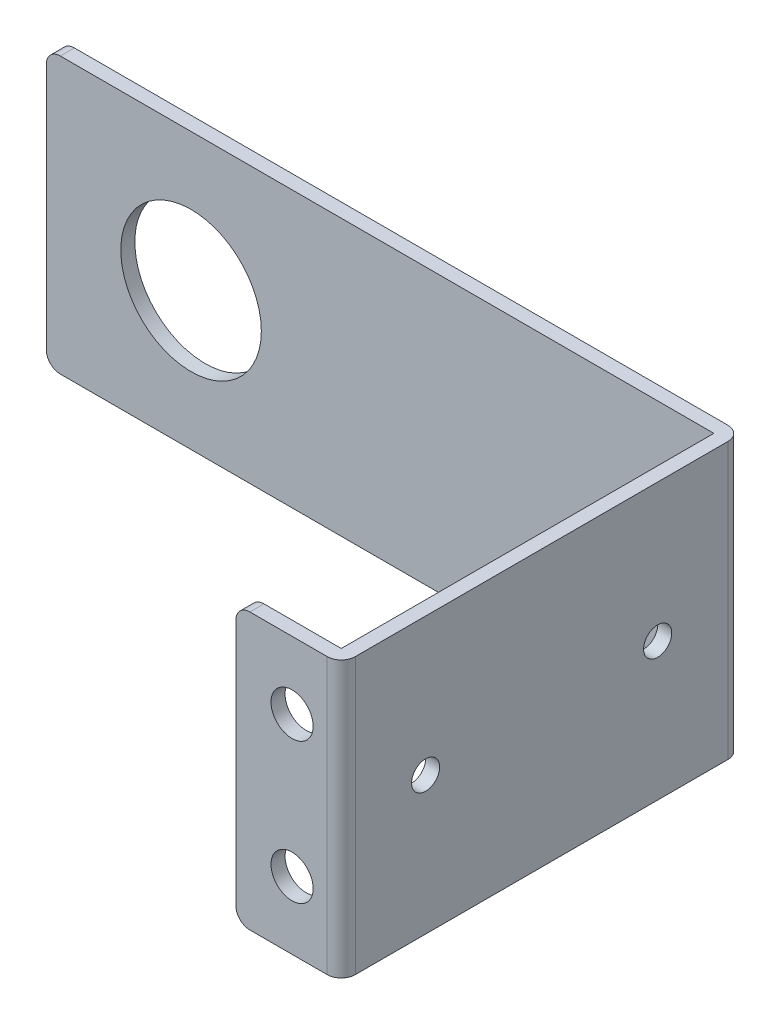
SolidWorks part; units mm, degrees
ref_plane "Front Plane" through (0, 0, 0) normal (0, 0, 1) x (1, 0, 0)
ref_plane "Top Plane" through (0, 0, 0) normal (0, 1, 0) x (1, 0, 0)
ref_plane "Right Plane" through (0, 0, 0) normal (1, 0, 0) x (0, 0, -1)
sketch "Sketch1" plane through (0, 0, 0) normal (0, 0, 1) x (1, 0, 0)
  line L1 (-23.75, -9.8) -> (23.75, -9.8)
  line L2 (-23.75, -9.8) -> (-23.75, 9.8)
  line L3 (-23.75, 9.8) -> (23.75, 9.8)
  line L4 (23.75, -9.8) -> (23.75, 9.8)
  line L5 (-23.75, -9.8) -> (23.75, 9.8) construction
  line L6 (-23.75, 9.8) -> (23.75, -9.8) construction
  circle A0 centre (-13.45, 0) radius 5
  point P0 (0, 0)
  dimension "D5" = 10
  dimension "D1" = 47.5
  dimension "D2" = 19.6
  dimension "D3" = 9.8
  dimension "D4" = 10.3
extrude "Boss-Extrude1" add sketch "Sketch1" along normal blind 1
sketch "Sketch2" plane through (0, 0, 1) normal (0, 0, 1) x (1, 0, 0)
  line L1 (23.75, 9.8) -> (24.75, 9.8)
  line L2 (23.75, 9.8) -> (23.75, -9.8)
  line L3 (23.75, -9.8) -> (24.75, -9.8)
  line L4 (24.75, 9.8) -> (24.75, -9.8)
  dimension "D1" = 1
extrude "Boss-Extrude2" add sketch "Sketch2" along normal blind 28.512 from offset 1 offset against normal yes
sketch "Sketch3" plane through (23.75, 0, 0) normal (-1, 0, 0) x (0, 0, 1)
  line L0 (28.512, -9.8) -> (1, -9.8) construction
  line L1 (28.512, 9.8) -> (27.512, 9.8)
  line L2 (28.512, 9.8) -> (28.512, -9.8)
  line L3 (28.512, -9.8) -> (27.512, -9.8)
  line L4 (27.512, 9.8) -> (27.512, -9.8)
  dimension "D1" = 1
extrude "Boss-Extrude3" add sketch "Sketch3" along normal blind 6.5
sketch "Sketch4" plane through (0, 0, 28.512) normal (0, 0, 1) x (1, 0, 0)
  line L0 (17.25, -9.8) -> (17.25, 9.8) construction
  line L1 (17.25, 0) -> (24.75, 0) construction
  line L2 (24.75, -9.8) -> (24.75, 9.8) construction
  circle A0 centre (21.25, 5) radius 1.5
  circle A1 centre (21.25, -5) radius 1.5
  dimension "D1" = 3
  dimension "D2" = 3
  dimension "D3" = 4
  dimension "D4" = 5
  dimension "D5" = 5
extrude "Cut-Extrude1" cut sketch "Sketch4" against normal up to next
sketch "Sketch6" plane through (23.75, 0, 0) normal (-1, 0, 0) x (0, 0, 1)
  line L0 (1, 9.8) -> (1, -9.8) construction
  line L1 (27.512, 9.8) -> (27.512, -9.8) construction
  circle A0 centre (6, 0) radius 1
  circle A1 centre (22.512, 0) radius 1
  dimension "D1" = 2
  dimension "D2" = 2
  dimension "D3" = 5
  dimension "D4" = 5
extrude "Cut-Extrude2" cut sketch "Sketch6" against normal blind 6.5
fillet "Fillet1" radius 1 6 edges at (-23.75, 9.8, 0.5) (-23.75, -9.8, 0.5) (17.25, -9.8, 28.012) (17.25, 9.8, 28.012) (24.75, 0, 0) (24.75, 0, 28.512)
